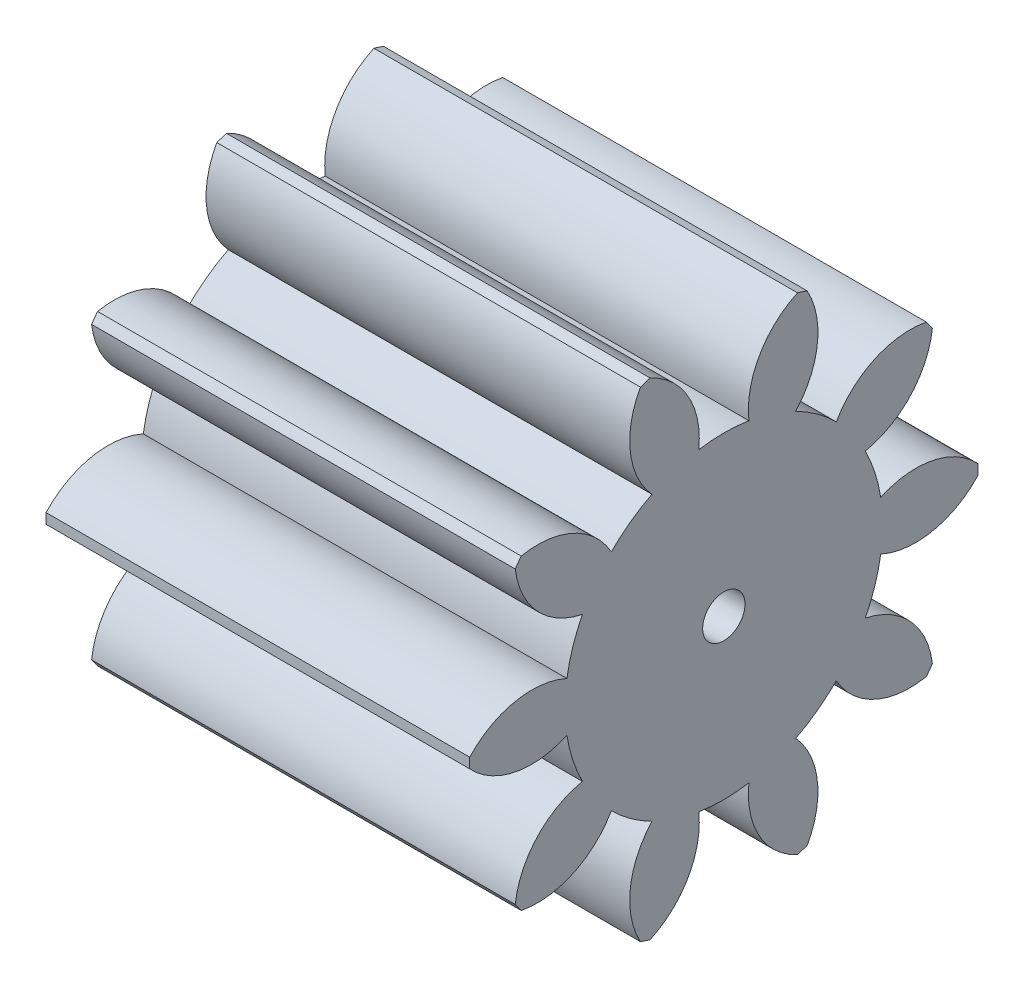
SolidWorks part; units mm, degrees
ref_plane "Plane1" through (0, 0, 0) normal (0, 0, 1) x (1, 0, 0)
ref_plane "Plane2" through (0, 0, 0) normal (0, 1, 0) x (1, 0, 0)
ref_plane "Plane3" through (0, 0, 0) normal (1, 0, 0) x (0, 0, -1)
sketch "HoldingSke" plane through (0, 0, 0) normal (0, 1, 0) x (1, 0, 0)
  line L0 (0, 0) -> (1.231, -0.2171)
  line L1 (-15, 0) -> (100, 0) construction
  line L2 (0, 0) -> (-2.1039, 2.3779)
  line L3 (0, 0) -> (-11.863, 4.5341)
  line L4 (0, 0) -> (8.5048, 1.4996)
  line L5 (0, 0) -> (-46.8476, -17.4728)
  line L6 (0, 0) -> (-6.6317, -4.4744)
  line L7 (-2.1039, 2.3779) -> (8.6586, 51.2059)
  line L8 (-76.2, 54.61) -> (-76.1, 54.61)
  line L9 (-71.009, 38.7566) -> (-53.1078, 45.2721)
  line L10 (-76.2, 71.12) -> (104.1128, 71.12)
  line L11 (0, 0) -> (-8, 0)
  line L12 (-76.2, 101.6) -> (-76.17, 101.6)
  line L13 (24.9733, 27.94) -> (52.9518, 28.4284)
  line L14 (24.9733, 27.94) -> (24.9743, 27.94)
  line L15 (24.9733, 27.94) -> (100.4006, 29.5858)
  line L16 (-63.627, -0.8) -> (-12.827, -0.8)
  circle A0 centre (0, 0) radius 0.4
  circle A1 centre (0, 0) radius 2.999
  circle A2 centre (0, 0) radius 37.5
  circle A3 centre (0, 0) radius 0.4
  dimension "MHD" = 5.998
  dimension "Hub_dia" = 75
  dimension "Bore" = 0.8
  dimension "MBD" = 0.8
  dimension "Num_teeth" = 10
  dimension "Pitch" = 1.25
  dimension "Overall_len" = 50
  dimension "Show_teeth" = 10
  dimension "Thickness" = 8
  dimension "OAL" = 50.0001
  dimension "T_dim" = 0.1
  dimension "Ap" = 20
  dimension "H" = 19.05
  dimension "Pitch_radius" = 180.3128
  dimension "Width" = 8
  dimension "Backlash" = 0.03
  dimension "Addendum_fac" = 1
  dimension "Dedendum_fac" = 1.25
  dimension "Clearance_fac" = 0.25
  dimension "Dedendum_add" = 0.001
  dimension "Module" = 0.8
sketch "BasProSke" plane through (0, 0, 0) normal (0, 1, 0) x (1, 0, 0)
  line L0 (-10, 0) -> (60, 0) construction
  line L1 (0, 0) -> (0, 4.8)
  line L2 (0, 0) -> (8, 0)
  line L3 (8, 0) -> (8, 4.8)
  line L4 (8, 4.8) -> (0, 4.8)
  dimension "Thickness" = 8
  dimension "Diameter" = 9.6
revolve "Base-Revolve" add sketch "BasProSke" angle 360 about L0
sketch "TooCutSke" plane through (0, 0, 0) normal (1, 0, 0) x (0, 0, -1)
  line L1 (0, 0) -> (0, 107) construction
  line L2 (0, 0) -> (-0.6781, 3.9421) construction
  line L3 (0, 0) -> (-2.4466, 7.5299) construction
  line L4 (-0.6781, 3.9421) -> (-1.2233, 3.765) construction
  arc A0 (0.4737, 2.9613) -> (-0.4737, 2.9613) centre (0, 0) ccw
  arc A1 (1.4269, 4.6096) -> (-1.4269, 4.6096) centre (0, 0) ccw
  circle A2 centre (0, 0) radius 4 construction
  circle A3 centre (0, 0) radius 3.7588 construction
  arc A4 (-0.4737, 2.9613) -> (-1.4269, 4.6096) centre (-2.0635, 3.1417) ccw
  arc A5 (1.4269, 4.6096) -> (0.4737, 2.9613) centre (2.0635, 3.1417) ccw
  dimension "Root_dia" = 5.998
  dimension "Overcut_dia" = 9.6508
  dimension "Pitch_dia" = 8
  dimension "Base_dia" = 7.5175
  dimension "Flank_rad" = 1.6
  dimension "Half_ang" = 18
  dimension "Half_CT" = 0.5732
extrude "ToothCut" cut sketch "TooCutSke" along normal through all
fillet "Breaks" [suppressed] radius 0.016
fillet "RootFillets" [suppressed] radius 0.201
pattern_circular "TeethCuts" count 10 every 36 about axis through (-10, 0, 0) along (1, 0, 0) of "ToothCut", "RootFillets", "Breaks"
sketch "HubNeaOneSke" plane through (0, 0, 0) normal (-1, 0, 0) x (0, 0, 1)
  circle A0 centre (0, 0) radius 2.999
  dimension "Diameter" = 5.998
extrude "HubNearOne" [suppressed] add sketch "HubNeaOneSke" along normal blind 42.0001
sketch "HubNeaBotSke" plane through (0, 0, 0) normal (-1, 0, 0) x (0, 0, 1)
  circle A0 centre (0, 0) radius 2.999
  dimension "Diameter" = 5.998
extrude "HubNearBoth" [suppressed] add sketch "HubNeaBotSke" along normal blind 21
ref_plane "FarPln" through (8, 0, 0) normal (1, 0, 0) x (0, 0, -1)
sketch "HubFarSke" plane through (8, 0, 0) normal (1, 0, 0) x (0, 0, -1)
  circle A0 centre (0, 0) radius 2.999
  dimension "Diameter" = 5.998
extrude "HubFar" [suppressed] add sketch "HubFarSke" along normal blind 21
sketch "BorSke" plane through (0, 0, 0) normal (1, 0, 0) x (0, 0, -1)
  circle A0 centre (0, 0) radius 0.4
  dimension "Diameter" = 0.8
extrude "Bore" cut sketch "BorSke" along normal mid plane 100.0001
sketch "KeySke" plane through (0, 0, 0) normal (1, 0, 0) x (0, 0, -1)
  line L0 (-0.05, 0) -> (-0.05, 0.5)
  line L1 (-0.05, 0.5) -> (0.05, 0.5)
  line L2 (0.05, 0.5) -> (0.05, 0)
  line L3 (0, 0) -> (0, 34) construction
  line L4 (-0.05, 0) -> (0.05, 0)
  dimension "Offset" = 0.5
  dimension "Width" = 0.1
extrude "Keyway" [suppressed] cut sketch "KeySke" along normal mid plane 100.0001
pattern_circular "Keyway2" [suppressed] count 2 every 90 about axis through (-10, 0, 0) along (1, 0, 0)
equation "' \"Module@HoldingSke\" = 6.35"
equation "' \"Num_teeth@HoldingSke\" = 12"
equation "' \"Ap@HoldingSke\" =  20"
equation "' \"Ap@HoldingSke\" = 20"
equation "' \"Width@HoldingSke\" = 0.5 * 25.4"
equation "' \"Hub_dia@HoldingSke\"= 1 * 25.4"
equation "' \"Hub_dia@HoldingSke\" = 1 * 25.4"
equation "' \"Overall_len@HoldingSke\" = 1.0 * 25.4"
equation "' \"Bore@HoldingSke\" = 0.75 * 25.4"
equation "' \"T_dim@HoldingSke\" = 0.1 * 25.4"
equation "' \"Width@KeySke\" = 0.25 * 25.4"
equation "' \"Show_teeth@HoldingSke\" = 13"
equation "' \"Backlash@HoldingSke\" = 0.009 * 25.4"
equation "' \"Addendum_fac@HoldingSke\" = 1.0"
equation "' \"Dedendum_fac@HoldingSke\" = 1.25"
equation "' \"Dedendum_add@HoldingSke\" = 0.00005 * 25.4"
equation "' \"Clearance_fac@HoldingSke\" = 0.25"
equation "\"Pitch@HoldingSke\" = 1 / \"Module@HoldingSke\""
equation "\"Overcut_dia@TooCutSke\" = (\"Num_teeth@HoldingSke\" + 2 * \"Addendum_fac@HoldingSke\") / \"Pitch@HoldingSke\" + 0.002 * 25.4"
equation "\"Pitch_dia@TooCutSke\" = \"Num_teeth@HoldingSke\" / \"Pitch@HoldingSke\""
equation "\"Base_dia@TooCutSke\" = \"Num_teeth@HoldingSke\" / \"Pitch@HoldingSke\" * cos((\"Ap@HoldingSke\"  * 3.14159265 / 180))"
equation "\"Root_dia@TooCutSke\" = (\"Num_teeth@HoldingSke\" + 2) / \"Pitch@HoldingSke\" - 2 * (\"Addendum_fac@HoldingSke\" + \"Dedendum_fac@HoldingSke\") / \"Pitch@HoldingSke\" - \"Dedendum_add@HoldingSke\" * 2"
equation "\"Half_ang@TooCutSke\" = 180 / \"Num_teeth@HoldingSke\""
equation "\"Half_CT@TooCutSke\" = \"Num_teeth@HoldingSke\" / \"Pitch@HoldingSke\" * sin((3.14159265 / 2 / \"Num_teeth@HoldingSke\")) / 2 - 7 * \"Backlash@HoldingSke\" / 4"
equation "\"Flank_rad@TooCutSke\" = \"Num_teeth@HoldingSke\" / \"Pitch@HoldingSke\" / 5"
equation "\"Radius@RootFillets\" = \"Clearance_fac@HoldingSke\" / \"Pitch@HoldingSke\" + \"Dedendum_add@HoldingSke\""
equation "\"Break_rad@Breaks\" = 0.02 / \"Pitch@HoldingSke\""
equation "\"Thickness@HoldingSke\" = \"Width@HoldingSke\""
equation "\"OAL@HoldingSke\" = \"Thickness@HoldingSke\""
equation "\"MHD@HoldingSke\" = (\"Num_teeth@HoldingSke\" + 2) / \"Pitch@HoldingSke\" - 2 * (\"Addendum_fac@HoldingSke\" + \"Dedendum_fac@HoldingSke\")  / \"Pitch@HoldingSke\" - \"Dedendum_add@HoldingSke\" * 2"
equation "\"MBD@HoldingSke\" = (\"Num_teeth@HoldingSke\" + 2) / \"Pitch@HoldingSke\" - 2 * (\"Addendum_fac@HoldingSke\" + \"Dedendum_fac@HoldingSke\")  / \"Pitch@HoldingSke\" - \"Dedendum_add@HoldingSke\" * 2 - 0.002 * 25.4"
equation "\"MHD@HoldingSke\" = ((sgn( \"MHD@HoldingSke\" - \"Hub_dia@HoldingSke\" )-1)*( \"MHD@HoldingSke\" - \"Hub_dia@HoldingSke\" ))/-2+ \"Hub_dia@HoldingSke\""
equation "\"MBD@HoldingSke\" = ((sgn( \"MBD@HoldingSke\" - \"Bore@HoldingSke\" )-1)*( \"MBD@HoldingSke\" - \"Bore@HoldingSke\" ))/-2+ \"Bore@HoldingSke\""
equation "\"OAL@HoldingSke\" = ((sgn( \"OAL@HoldingSke\" - \"Overall_len@HoldingSke\" )+1)*( \"OAL@HoldingSke\" - \"Overall_len@HoldingSke\" ))/2 + \"Overall_len@HoldingSke\" + 0.000002 * 25.4"
equation "\"Num_teeth@TeethCuts\" = int( \"Show_teeth@HoldingSke\" ) + 1"
equation "\"Num_teeth@TeethCuts\" = ((sgn( \"Num_teeth@TeethCuts\" - \"Num_teeth@HoldingSke\" )-1)*( \"Num_teeth@TeethCuts\" - \"Num_teeth@HoldingSke\" ))/-2+ \"Num_teeth@HoldingSke\""
equation "\"Num_teeth@TeethCuts\" = ((sgn( \"Num_teeth@TeethCuts\" - 2.0)+1)*( \"Num_teeth@TeethCuts\" - 2.0))/2 +2.0"
equation "\"Angle@TeethCuts\" = 360.0 / \"Num_teeth@HoldingSke\""
equation "\"Diameter@BasProSke\" = (\"Num_teeth@HoldingSke\" + 2 * \"Addendum_fac@HoldingSke\") / \"Pitch@HoldingSke\""
equation "\"Thickness@BasProSke\"  = \"Thickness@HoldingSke\""
equation "' \"Fillet_rad@BasProSke\" =  \"Thickness@HoldingSke\" * 0.05"
equation "' \"Fillet_rad@BasProSke\" = \"Thickness@HoldingSke\" * 0.05"
equation "\"MHD@HoldingSke\" = ((sgn( \"MHD@HoldingSke\" - \"Root_dia@TooCutSke\" )-1)*( \"MHD@HoldingSke\" - \"Root_dia@TooCutSke\" ))/-2+ \"Root_dia@TooCutSke\""
equation "\"Diameter@HubNeaOneSke\" = \"MHD@HoldingSke\""
equation "\"Length@HubNearOne\" = \"OAL@HoldingSke\" - \"Thickness@BasProSke\""
equation "\"Diameter@HubNeaBotSke\" = \"MHD@HoldingSke\""
equation "\"Length@HubNearBoth\" = ( \"OAL@HoldingSke\" - \"Thickness@BasProSke\" ) / 2.0"
equation "\"Thickness@FarPln\" = \"Thickness@BasProSke\""
equation "\"Diameter@HubFarSke\" = \"MHD@HoldingSke\""
equation "\"Length@HubFar\" = ( \"OAL@HoldingSke\" - \"Thickness@BasProSke\" ) / 2.0"
equation "\"Diameter@BorSke\" = \"MBD@HoldingSke\""
equation "\"D1@Bore\" = \"OAL@HoldingSke\" * 2.0"
equation "\"D1@Keyway\" = \"OAL@HoldingSke\" * 2.0"
equation "\"Offset@KeySke\" = \"T_dim@HoldingSke\" + \"MBD@HoldingSke\" / 2.0"
